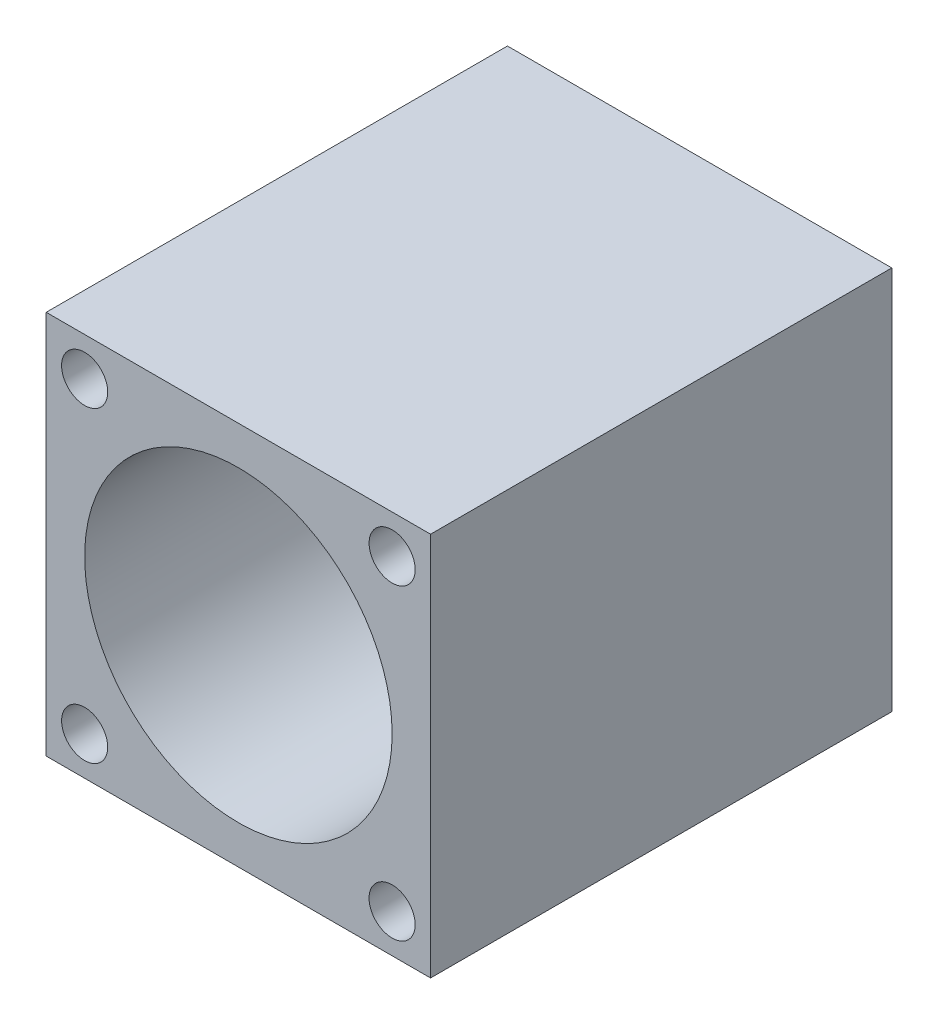
SolidWorks part; units mm, degrees
ref_plane "Plan de face" through (0, 0, 0) normal (0, 0, 1) x (1, 0, 0)
ref_plane "Plan de dessus" through (0, 0, 0) normal (0, 1, 0) x (1, 0, 0)
ref_plane "Plan de droite" through (0, 0, 0) normal (1, 0, 0) x (0, 0, -1)
sketch "Esquisse1" plane through (0, 0, 0) normal (0, 0, 1) x (1, 0, 0)
  line L0 (12.5, -12.5) -> (12.5, 12.5)
  line L1 (-12.5, 12.5) -> (12.5, 12.5)
  line L2 (-10, -10) -> (10, -10) construction
  line L3 (-12.5, -12.5) -> (-12.5, 12.5)
  line L6 (-12.5, -12.5) -> (12.5, -12.5)
  circle A0 centre (10, 10) radius 1.5
  circle A1 centre (0, 0) radius 3
  circle A2 centre (-10, 10) radius 1.5
  circle A3 centre (10, -10) radius 1.5
  circle A4 centre (-10, -10) radius 1.5
  dimension "D1" = 12.5
  dimension "D2" = 20
  dimension "D3" = 20
  dimension "D4" = 10
  dimension "D5" = 20
extrude "Extrusion3" add sketch "Esquisse1" along normal blind 30
sketch "Esquisse7" plane through (0, 0, 30) normal (0, 0, 1) x (1, 0, 0)
  circle A0 centre (0, 0) radius 10
sketch "Esquisse8" plane through (0, 0, 30) normal (0, 0, 1) x (1, 0, 0)
  circle A0 centre (0, 0) radius 10
extrude "Extrusion4" cut sketch "Esquisse8" against normal blind 28
